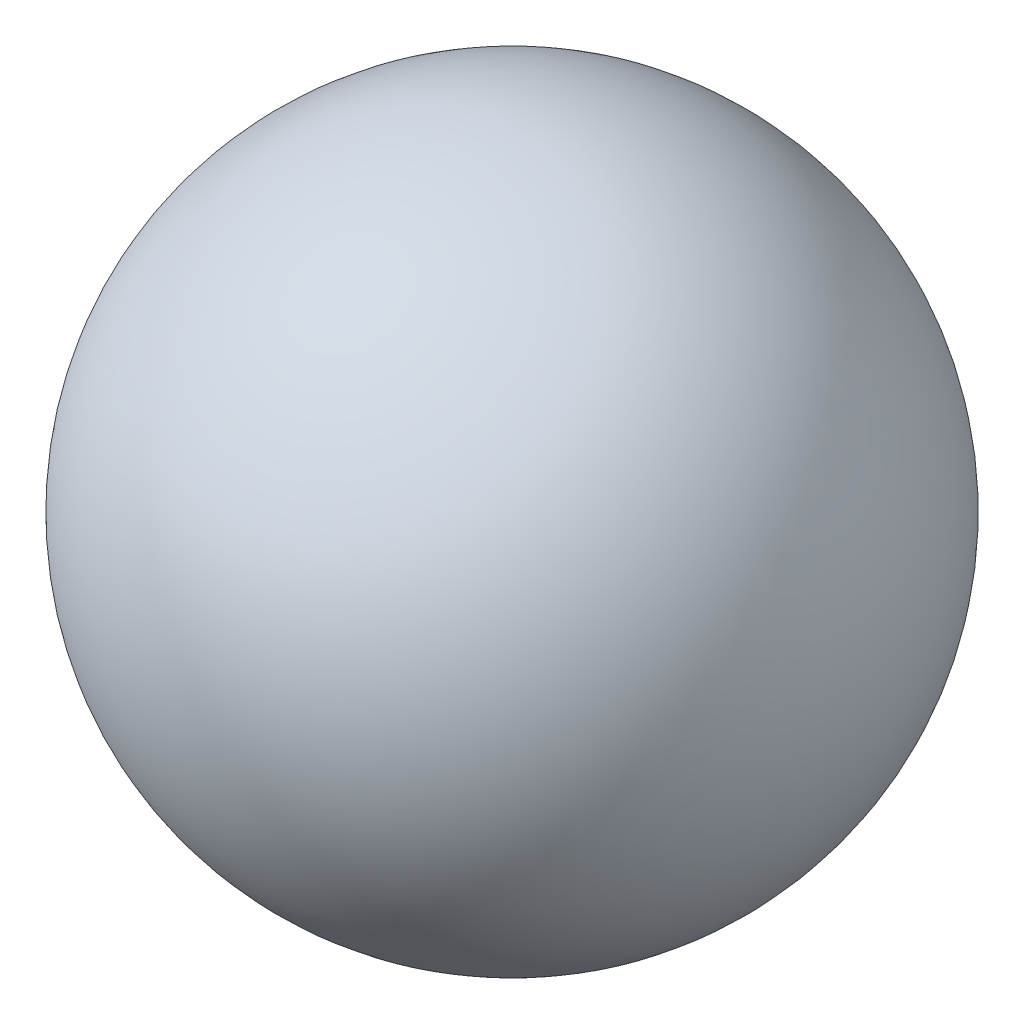
SolidWorks part; units mm, degrees
ref_plane "Plan de face" through (0, 0, 0) normal (0, 0, 1) x (1, 0, 0)
ref_plane "Plan de dessus" through (0, 0, 0) normal (0, 1, 0) x (1, 0, 0)
ref_plane "Plan de droite" through (0, 0, 0) normal (1, 0, 0) x (0, 0, -1)
sketch "Esquisse1" plane through (0, 0, 0) normal (0, 0, 1) x (1, 0, 0)
  line L0 (0, 30) -> (0, -30)
  arc A0 (0, 30) -> (0, -30) centre (0, 0) ccw
  dimension "D1" = 60
revolve "Révolution1" add sketch "Esquisse1" angle 360 about L0
